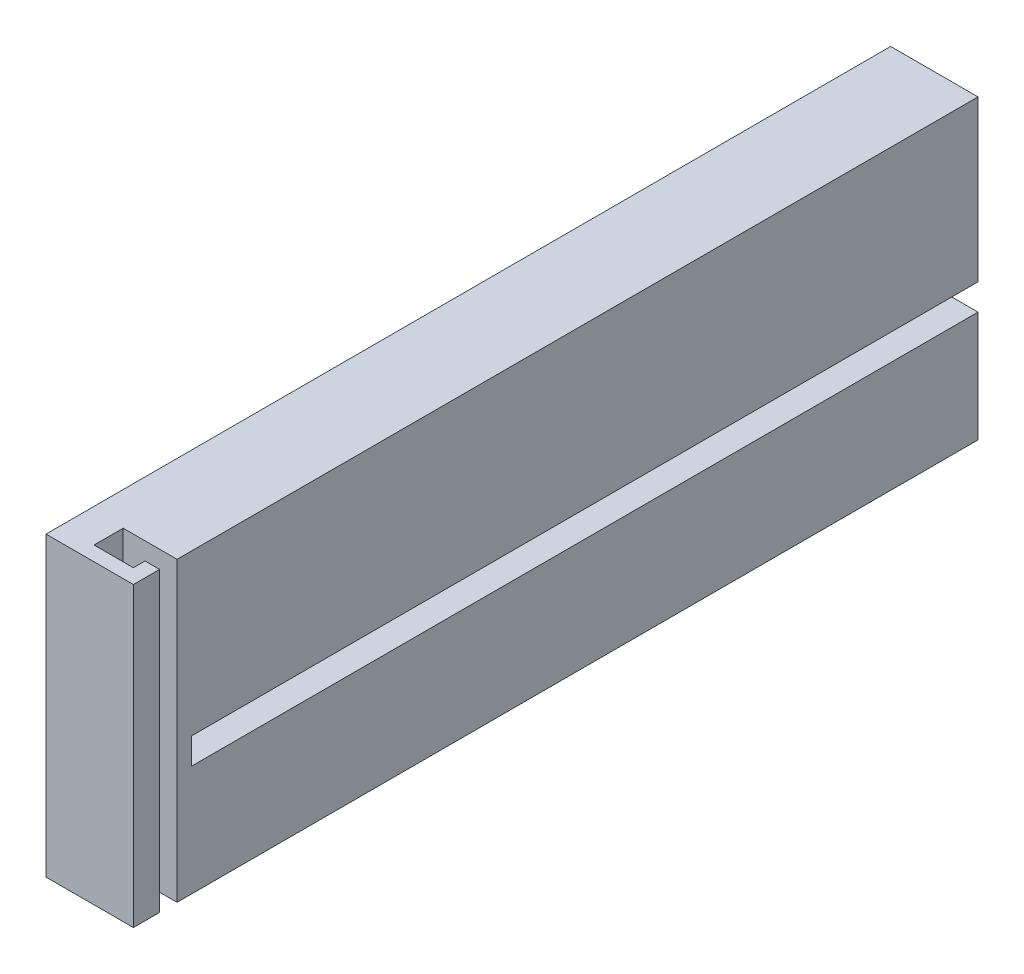
SolidWorks part; units mm, degrees
ref_plane "Front Plane" through (0, 0, 0) normal (0, 0, 1) x (1, 0, 0)
ref_plane "Top Plane" through (0, 0, 0) normal (0, 1, 0) x (1, 0, 0)
ref_plane "Right Plane" through (0, 0, 0) normal (1, 0, 0) x (0, 0, -1)
sketch "Sketch1" plane through (0, 0, 0) normal (1, 0, 0) x (0, 0, -1)
  line L1 (-64.5621, 30.5573) -> (80.4379, 30.5573)
  line L2 (-64.5621, 30.5573) -> (-64.5621, -20.4427)
  line L3 (-64.5621, -20.4427) -> (80.4379, -20.4427)
  line L4 (80.4379, 30.5573) -> (80.4379, -20.4427)
  dimension "D1" = 145
  dimension "D2" = 51
extrude "Boss-Extrude1" add sketch "Sketch1" along normal blind 15 contours L2 L3 L4 L1
sketch "Sketch2" plane through (0, 0, 64.5621) normal (0, 0, 1) x (1, 0, 0)
  line L0 (15, -6.9427) -> (15, -20.4427)
  line L2 (15, 30.5573) -> (15, -20.4427) construction
  line L4 (15, -6.9427) -> (10, -6.9427)
  line L5 (15, -6.9427) -> (15, -2.7427)
  line L6 (15, -2.7427) -> (10, -2.7427)
  line L7 (10, -6.9427) -> (10, -2.7427)
  dimension "D1" = 13.5
  dimension "D2" = 5
  dimension "D3" = 4.2
sketch "Sketch6" plane through (0, 30.5573, 0) normal (0, 1, 0) x (1, 0, 0)
  line L0 (15, -64.5621) -> (15, -60.0621)
  line L1 (15, -64.5621) -> (15, 80.4379) construction
  line L2 (15, -60.0621) -> (15, -57.0621)
  line L3 (15, -57.0621) -> (12.5, -57.0621)
  line L4 (12.5, -57.0621) -> (5.75, -57.0621)
  line L5 (5.75, -57.0621) -> (5.75, -62.0621)
  line L6 (5.75, -62.0621) -> (12.5, -62.0621)
  line L7 (12.5, -62.0621) -> (12.5, -60.0621)
  line L8 (12.5, -60.0621) -> (15, -60.0621)
  line M11 (15, -64.5621) -> (15, 80.4379)
  dimension "D1" = 4.5
  dimension "D2" = 3
  dimension "D3" = 2.5
  dimension "D4" = 6.75
  dimension "D5" = 5
extrude "Cut-Extrude3" cut sketch "Sketch6" against normal through all contours L7 L8 L3 L4 L5 L6 M11
sketch "Sketch7" plane through (0, 0, -80.4379) normal (0, 0, -1) x (-1, 0, 0)
  line L0 (-15, -20.4427) -> (-15, -1.4427)
  line L2 (-10, 3.0573) -> (-15, 3.0573)
  line L3 (-10, 3.0573) -> (-10, -1.4427)
  line L4 (-10, -1.4427) -> (-15, -1.4427)
  line L5 (-15, 3.0573) -> (-15, -1.4427)
  point P2 (0, 0)
  line M6 (-15, 30.5573) -> (-15, -20.4427)
  dimension "D1" = 19
  dimension "D2" = 5
  dimension "D3" = 4.5
extrude "Cut-Extrude5" cut sketch "Sketch7" against normal blind 135 contours L4 L3 L2 M6
